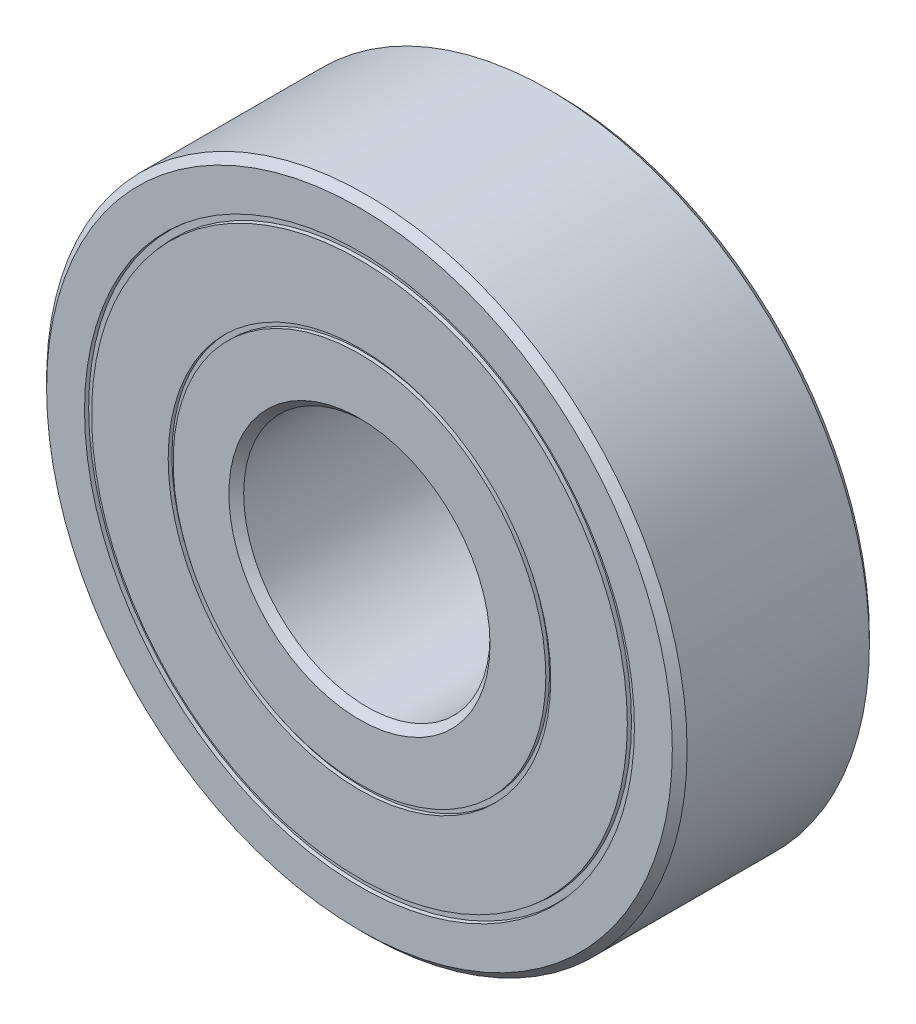
SolidWorks part; units mm, degrees
ref_plane "Alzado" through (0, 0, 0) normal (0, 0, 1) x (1, 0, 0)
ref_plane "Planta" through (0, 0, 0) normal (0, 1, 0) x (1, 0, 0)
ref_plane "Vista lateral" through (0, 0, 0) normal (1, 0, 0) x (0, 0, -1)
sketch "Croquis1" plane through (0, 0, 0) normal (0, 0, 1) x (1, 0, 0)
  circle A0 centre (0, 0) radius 5
  circle A1 centre (0, 0) radius 13
  dimension "D1" = 10
  dimension "D2" = 26
extrude "Saliente-Extruir1" add sketch "Croquis1" along normal blind 8
chamfer "Chaflán1" distance 0.3 angle 45 4 edges at (13, 0, 0) (13, 0, 8) (5, 0, 8) (5, 0, 0)
sketch "Croquis2" plane through (0, 0, 0) normal (1, 0, 0) x (0, 0, -1)
  line L0 (-8.85, 11.2675) -> (-7.85, 11.1425)
  line L1 (-7.85, 11.1425) -> (-7.85, 10.8925)
  line L2 (-7.85, 10.8925) -> (-8.85, 10.7675)
  line L3 (-8.85, 10.7675) -> (-8.85, 11.2675)
  line L4 (-7.1588, 11.0175) -> (-4.5217, 11.0175) construction
  line L5 (-4, 12.5365) -> (-4, -11.2918) construction
  line L6 (-7.7, -13) -> (-7.7, 13) construction
  line L7 (-0.3, 13) -> (-0.3, -13) construction
  line L8 (-8, 12.7) -> (-8, -12.7) construction
  line L9 (0.85, 10.7675) -> (0.85, 11.2675)
  line L10 (-0.15, 10.8925) -> (0.85, 10.7675)
  line L11 (-0.15, 11.1425) -> (-0.15, 10.8925)
  line L12 (0.85, 11.2675) -> (-0.15, 11.1425)
  line L13 (-8.85, 7.7651) -> (-7.85, 7.7651)
  line L14 (-8.85, 7.7651) -> (-8.85, 7.5651)
  line L15 (-8.85, 7.5651) -> (-7.85, 7.5651)
  line L16 (-7.85, 7.7651) -> (-7.85, 7.5651)
  line L17 (-0.15, 7.7651) -> (-0.15, 7.5651)
  line L18 (0.85, 7.5651) -> (-0.15, 7.5651)
  line L19 (0.85, 7.7651) -> (0.85, 7.5651)
  line L20 (0.85, 7.7651) -> (-0.15, 7.7651)
  dimension "D1" = 0.25
  dimension "D2" = 0.5
  dimension "D3" = 0.15
  dimension "D5" = 1
  dimension "D6" = 0.2
sketch "Croquis3" plane through (0, 0, 0) normal (1, 0, 0) x (0, 0, -1)
  line L0 (-12.4113, 0) -> (6.9361, 0) construction
revolve "Cortar-Revolución1" cut sketch "Croquis2" angle 360 about L0
